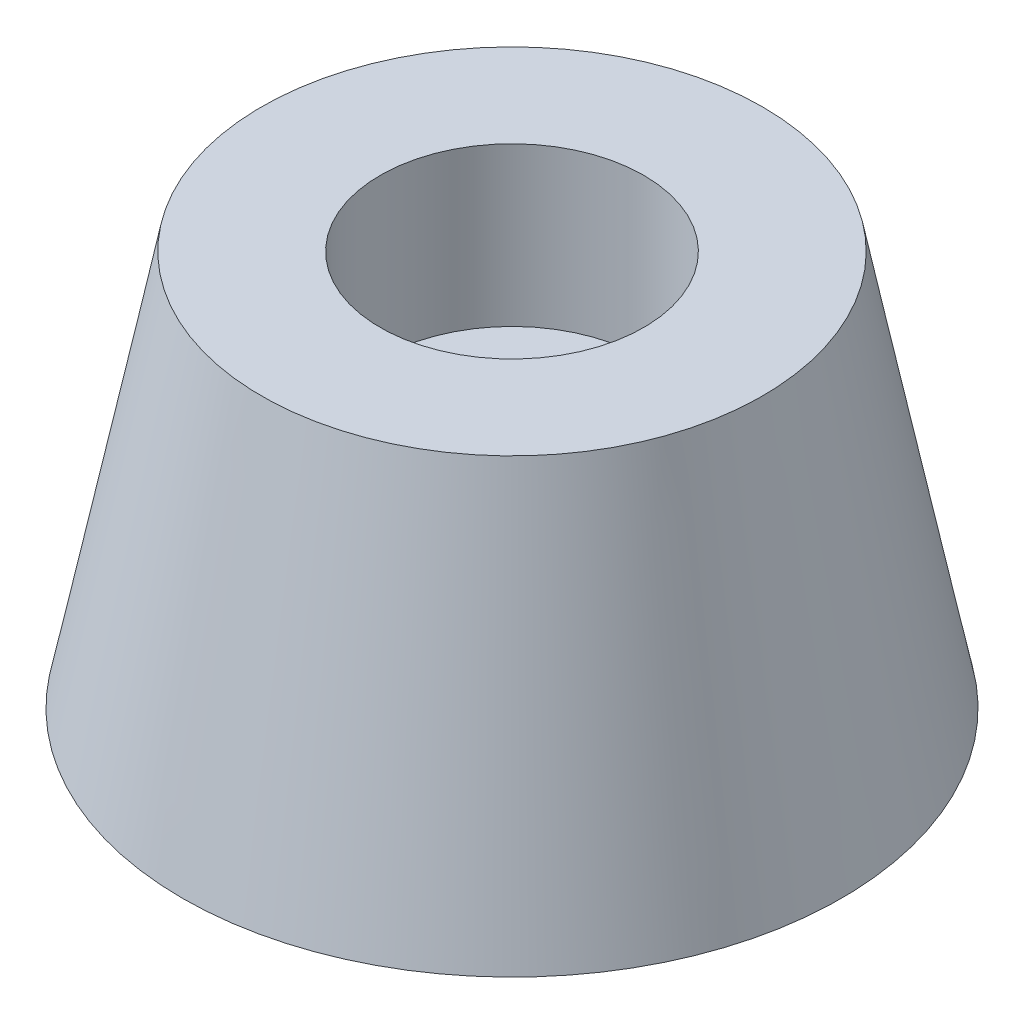
SolidWorks part; units mm, degrees
material "硅橡胶"
ref_plane "前视基准面" through (0, 0, 0) normal (0, 0, 1) x (1, 0, 0)
ref_plane "上视基准面" through (0, 0, 0) normal (0, 1, 0) x (1, 0, 0)
ref_plane "右视基准面" through (0, 0, 0) normal (1, 0, 0) x (0, 0, -1)
sketch "草图1" plane through (0, 0, 0) normal (0, 0, 1) x (1, 0, 0)
  line L0 (0, 0) -> (0, 29.8578) construction
  line L1 (-9.5, 15) -> (-12.5, 0)
  line L2 (-12.5, 0) -> (-2.5, 0)
  line L3 (-2.5, 0) -> (-2.5, 9)
  line L4 (-2.5, 9) -> (-5, 9)
  line L5 (-5, 9) -> (-5, 15)
  line L6 (-5, 15) -> (-9.5, 15)
  point P5 (-5, 12)
  dimension "D1" = 9.5
  dimension "D2" = 12.5
  dimension "D3" = 15
  dimension "D4" = 2.5
  dimension "D5" = 5
  dimension "D6" = 6
revolve "旋转1" add sketch "草图1" angle 360 about L0
